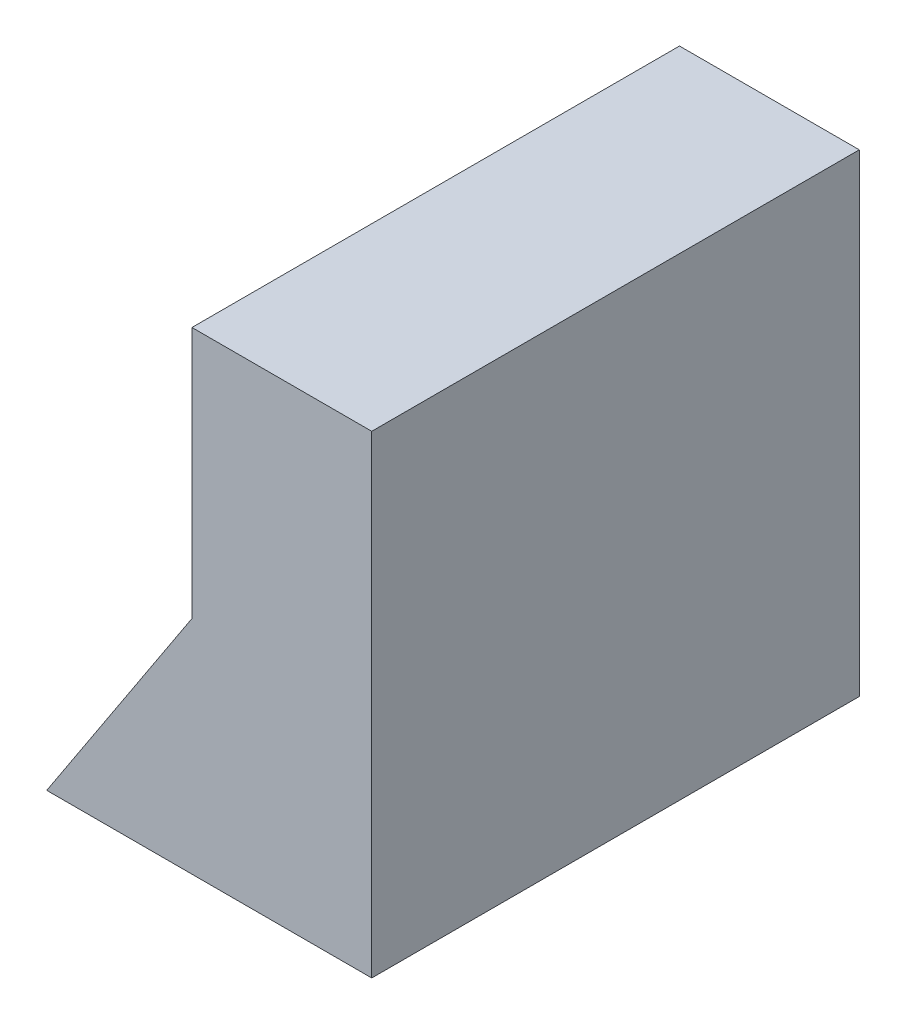
SolidWorks part; units mm, degrees
ref_plane "Front Plane" through (0, 0, 0) normal (0, 0, 1) x (1, 0, 0)
ref_plane "Top Plane" through (0, 0, 0) normal (0, 1, 0) x (1, 0, 0)
ref_plane "Right Plane" through (0, 0, 0) normal (1, 0, 0) x (0, 0, -1)
sketch "Sketch1" plane through (0, 0, 0) normal (0, 0, 1) x (1, 0, 0)
  line L0 (18.9661, 20.3044) -> (24.328, 28.4789)
  line L1 (24.328, 28.4789) -> (24.328, 37.7855)
  line L2 (24.328, 37.7855) -> (30.9661, 37.7855)
  line L3 (30.9661, 37.7855) -> (30.9661, 28.4789)
  line L5 (30.9661, 28.4789) -> (30.9661, 20.3044)
  line L6 (30.9661, 20.3044) -> (18.9661, 20.3044)
  dimension "D1" = 9.3066
  dimension "D2" = 6.6381
extrude "Boss-Extrude1" add sketch "Sketch1" along normal mid plane 18 contours L2 L3 L5 L6 L0 L1
